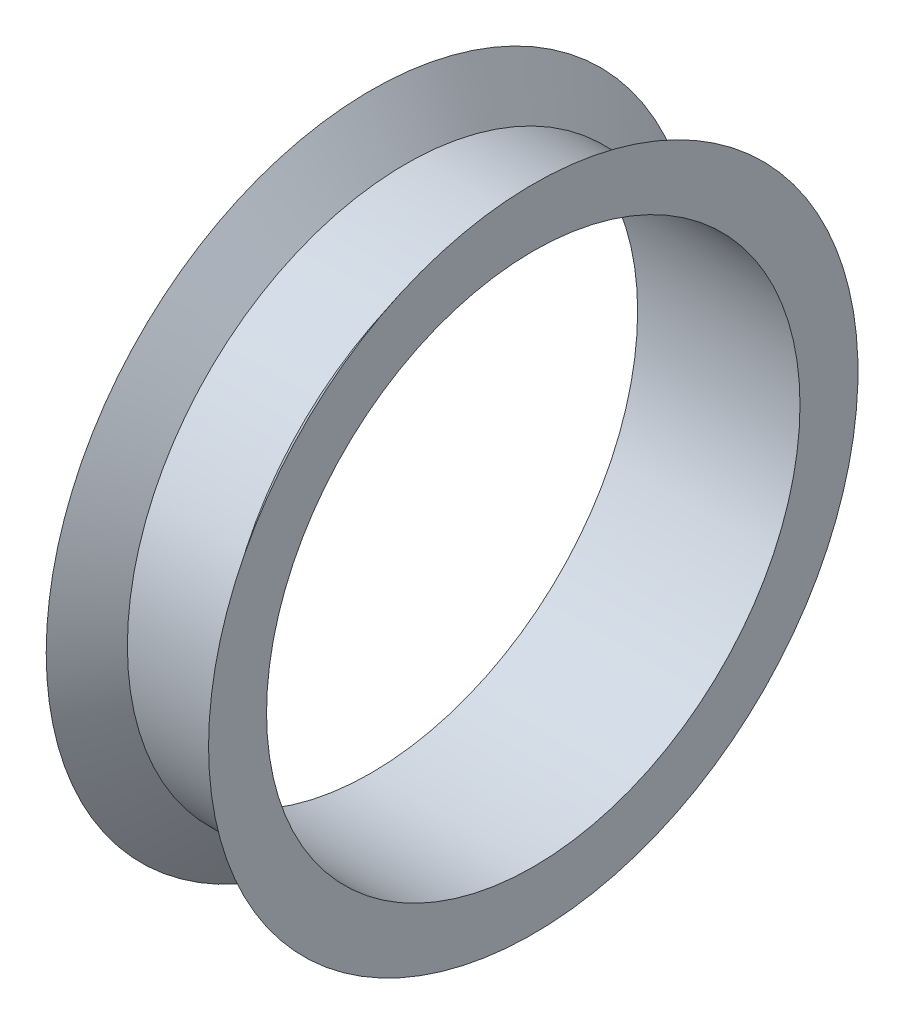
SolidWorks part; units mm, degrees
ref_plane "Front Plane" through (0, 0, 0) normal (0, 0, 1) x (1, 0, 0)
ref_plane "Top Plane" through (0, 0, 0) normal (0, 1, 0) x (1, 0, 0)
ref_plane "Right Plane" through (0, 0, 0) normal (1, 0, 0) x (0, 0, -1)
sketch "Sketch1" plane through (0, 0, 0) normal (0, 1, 0) x (1, 0, 0)
  line L0 (-2.1969, 5.3814) -> (-2.1969, 8.3814)
  line L1 (-2.1969, 8.3814) -> (-0.6969, 6.3814)
  line L2 (-0.6969, 6.3814) -> (3.3031, 6.3814)
  line L3 (3.3031, 6.3814) -> (4.8031, 8.3814)
  line L4 (4.8031, 8.3814) -> (4.8031, 5.3814)
  line L5 (4.8031, 5.3814) -> (-2.1969, 5.3814)
  line L6 (-2.1969, -5.6186) -> (4.8031, -5.6186) construction
  dimension "D1" = 7
  dimension "D2" = 1.5
  dimension "D3" = 1.5
  dimension "D4" = 1
  dimension "D5" = 3
  dimension "D6" = 3
  dimension "D7" = 11
revolve "Revolve1" add sketch "Sketch1" angle 360 about L6
sketch "Sketch2" plane through (4.8031, 0, 0) normal (1, 0, 0) x (0, 0, -1)
  circle A0 centre (-5.6186, 0) radius 11.5
  dimension "D1" = 23
extrude "Cut-Extrude1" cut sketch "Sketch2" against normal blind 10
